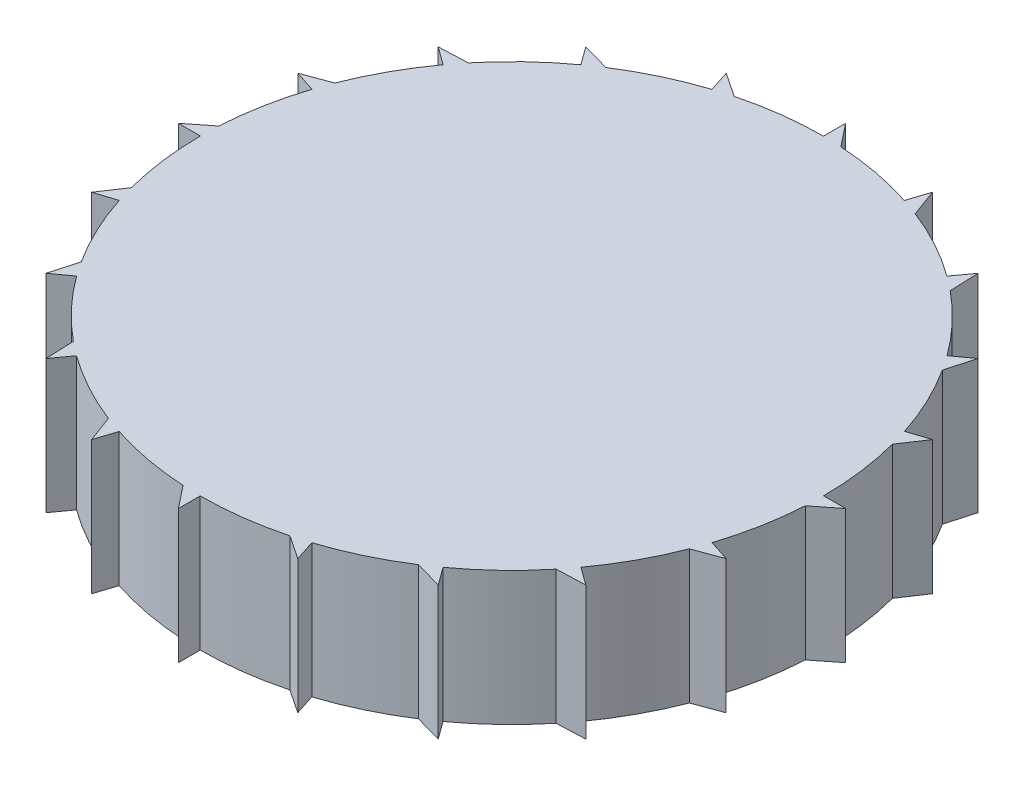
SolidWorks part; units mm, degrees
ref_plane "Front Plane" through (0, 0, 0) normal (0, 0, 1) x (1, 0, 0)
ref_plane "Top Plane" through (0, 0, 0) normal (0, 1, 0) x (1, 0, 0)
ref_plane "Right Plane" through (0, 0, 0) normal (1, 0, 0) x (0, 0, -1)
sketch "Sketch1" plane through (0, 0, 0) normal (0, 1, 0) x (1, 0, 0)
  circle A0 centre (0, 0) radius 70
  dimension "D1" = 140
extrude "Boss-Extrude1" add sketch "Sketch1" along normal blind 30
sketch "Sketch2" plane through (0, 0, 0) normal (0, 1, 0) x (1, 0, 0)
  line L0 (-5, 0) -> (5, 0)
  line L1 (5, 0) -> (5, 10)
  line L3 (-5, 10) -> (-5, 0)
  line L4 (-5, 10) -> (0, 18.9908)
  line L5 (0, 18.9908) -> (5, 10)
  dimension "D1" = 5
  dimension "D2" = 10
  dimension "D3" = 10
extrude "Boss-Extrude2" add sketch "Sketch2" against normal blind 30
sketch "Sketch3" plane through (0, 30, 0) normal (0, 1, 0) x (1, 0, 0)
  line L0 (0, 70) -> (0, 75)
  line L1 (0, 75) -> (4.0423, 69.8832)
  circle A0 centre (0, 0) radius 70 construction
  circle A1 centre (0, 0) radius 120
  circle M3 centre (0, 0) radius 70
  dimension "D1" = 5
extrude "Boss-Extrude3" add sketch "Sketch3" against normal blind 30 contours L1 L0 M3
pattern_circular "CirPattern1" count 20 over 360 about axis through (0.0009, 0, -0.0466) along (0, 1, 0) of "Boss-Extrude3"
